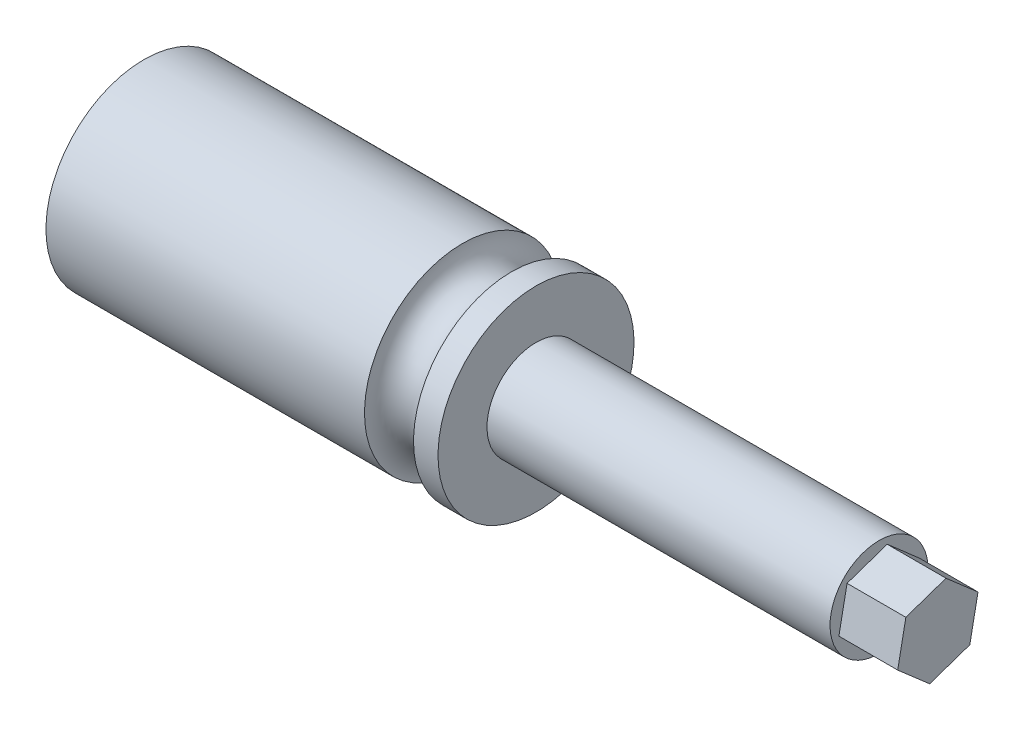
SolidWorks part; units mm, degrees
ref_plane "Front Plane" through (0, 0, 0) normal (0, 0, 1) x (1, 0, 0)
ref_plane "Top Plane" through (0, 0, 0) normal (0, 1, 0) x (1, 0, 0)
ref_plane "Right Plane" through (0, 0, 0) normal (1, 0, 0) x (0, 0, -1)
sketch "Sketch1" plane through (0, 0, 0) normal (0, 0, 1) x (1, 0, 0)
  line L1 (0, 0) -> (-101.6, 0)
  line L2 (0, 12.7) -> (0, 25.4)
  line L3 (0, 25.4) -> (-6.35, 25.4)
  line L4 (-101.6, 0) -> (-101.6, 25.4)
  line L5 (-19.05, 25.4) -> (-101.6, 25.4)
  line L7 (0, 0) -> (88.9, 0)
  line L9 (0, 12.7) -> (88.9, 12.7)
  line L10 (88.9, 0) -> (88.9, 12.7)
  arc A0 (-19.05, 25.4) -> (-6.35, 25.4) centre (-12.7, 25.4) ccw
revolve "Revolve1" add sketch "Sketch1" angle 360 about L1
sketch "Sketch2" plane through (88.9, 0, 0) normal (1, 0, 0) x (0, 0, -1)
  line L1 (8.2882, -7.23) -> (10.4055, 3.5628)
  line L2 (10.4055, 3.5628) -> (2.1173, 10.7928)
  line L3 (2.1173, 10.7928) -> (-8.2882, 7.23)
  line L4 (-8.2882, 7.23) -> (-10.4055, -3.5628)
  line L5 (-10.4055, -3.5628) -> (-2.1173, -10.7928)
  line L6 (-2.1173, -10.7928) -> (8.2882, -7.23)
  circle A0 centre (0, 0) radius 9.525 construction
extrude "Boss-Extrude1" add sketch "Sketch2" along normal blind 15.24
sketch3d "URDF Reference"
  line L0 (0, 0, 0) -> (10, 0, 0) construction
  line L1 (0, 0, 0) -> (0, 0, -10) construction
  point P0 (0, 0, 0)
